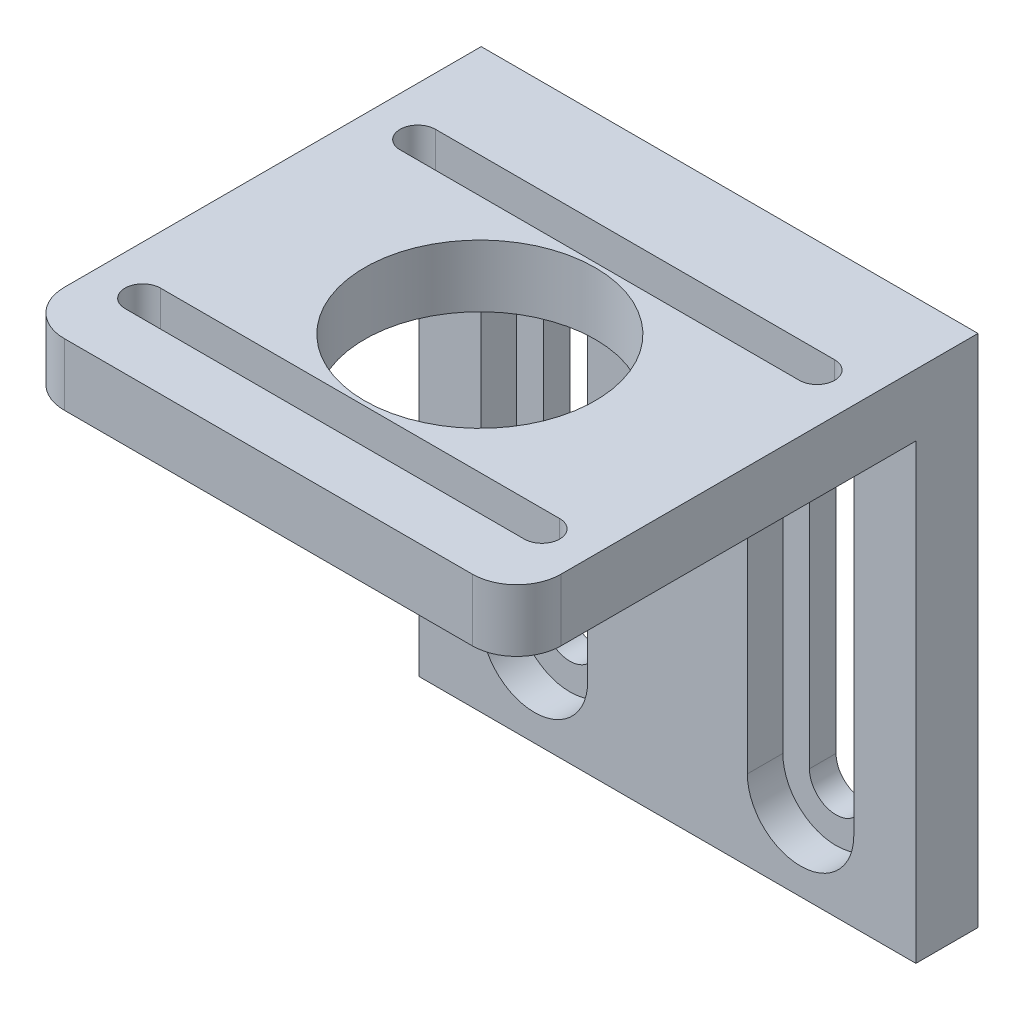
SolidWorks part; units mm, degrees
ref_plane "Front Plane" through (0, 0, 0) normal (0, 0, 1) x (1, 0, 0)
ref_plane "Top Plane" through (0, 0, 0) normal (0, 1, 0) x (1, 0, 0)
ref_plane "Right Plane" through (0, 0, 0) normal (1, 0, 0) x (0, 0, -1)
sketch "Esboço1" plane through (0, 0, 0) normal (0, 0, 1) x (1, 0, 0)
  line L32 (-63.6703, 183.4684) -> (-63.6703, 125.4684)
  line L33 (-63.6703, 125.4684) -> (-7.6703, 125.4684)
  line L34 (-7.6703, 125.4684) -> (-7.6703, 183.4684)
  line L35 (-7.6703, 183.4684) -> (-63.6703, 183.4684)
extrude "Ressalto-extrusão1" add sketch "Esboço1" along normal blind 7
sketch "Esboço3" plane through (0, 0, 7) normal (0, 0, 1) x (1, 0, 0)
  line L14 (-47.6703, 134.4684) -> (-47.6703, 171.4684)
  line L15 (-53.6703, 171.4684) -> (-53.6703, 134.4684)
  line L16 (-47.6703, 134.4684) -> (-47.6703, 171.4684)
  line L17 (-53.6703, 171.4684) -> (-53.6703, 134.4684)
  line L31 (-23.6703, 171.4684) -> (-23.6703, 134.4684)
  line L32 (-17.6703, 134.4684) -> (-17.6703, 171.4684)
  line L33 (-23.6703, 171.4684) -> (-23.6703, 134.4684)
  line L34 (-17.6703, 134.4684) -> (-17.6703, 171.4684)
  arc A21 (-48.4342, 173.4684) -> (-50.6703, 174.4684) centre (-50.6703, 171.4684) ccw
  arc A22 (-47.6703, 171.4684) -> (-48.4342, 173.4684) centre (-50.6703, 171.4684) ccw
  arc A23 (-50.6703, 174.4684) -> (-52.9064, 173.4684) centre (-50.6703, 171.4684) ccw
  arc A24 (-52.9064, 173.4684) -> (-53.6703, 171.4684) centre (-50.6703, 171.4684) ccw
  arc A25 (-53.6703, 134.4684) -> (-47.6703, 134.4684) centre (-50.6703, 134.4684) ccw
  arc A26 (-48.4342, 173.4684) -> (-50.6703, 174.4684) centre (-50.6703, 171.4684) ccw
  arc A27 (-47.6703, 171.4684) -> (-48.4342, 173.4684) centre (-50.6703, 171.4684) ccw
  arc A28 (-50.6703, 174.4684) -> (-52.9064, 173.4684) centre (-50.6703, 171.4684) ccw
  arc A29 (-52.9064, 173.4684) -> (-53.6703, 171.4684) centre (-50.6703, 171.4684) ccw
  arc A30 (-53.6703, 134.4684) -> (-47.6703, 134.4684) centre (-50.6703, 134.4684) ccw
  arc A46 (-18.4342, 173.4684) -> (-20.6703, 174.4684) centre (-20.6703, 171.4684) ccw
  arc A47 (-17.6703, 171.4684) -> (-18.4342, 173.4684) centre (-20.6703, 171.4684) ccw
  arc A48 (-20.6703, 174.4684) -> (-22.9064, 173.4684) centre (-20.6703, 171.4684) ccw
  arc A49 (-22.9064, 173.4684) -> (-23.6703, 171.4684) centre (-20.6703, 171.4684) ccw
  arc A50 (-23.6703, 134.4684) -> (-17.6703, 134.4684) centre (-20.6703, 134.4684) ccw
  arc A51 (-18.4342, 173.4684) -> (-20.6703, 174.4684) centre (-20.6703, 171.4684) ccw
  arc A52 (-17.6703, 171.4684) -> (-18.4342, 173.4684) centre (-20.6703, 171.4684) ccw
  arc A53 (-20.6703, 174.4684) -> (-22.9064, 173.4684) centre (-20.6703, 171.4684) ccw
  arc A54 (-22.9064, 173.4684) -> (-23.6703, 171.4684) centre (-20.6703, 171.4684) ccw
  arc A55 (-23.6703, 134.4684) -> (-17.6703, 134.4684) centre (-20.6703, 134.4684) ccw
  dimension "D1" = 0
  dimension "D2" = 0
extrude "Corte-extrusão1" cut sketch "Esboço3" against normal blind 7
sketch "Esboço4" plane through (0, 0, 7) normal (0, 0, 1) x (1, 0, 0)
  line L0 (-7.6703, 125.4684) -> (-7.6703, 183.4684) construction
  line L1 (-63.6703, 183.4684) -> (-7.6703, 183.4684)
  line L2 (-63.6703, 183.4684) -> (-63.6703, 176.4684)
  line L3 (-63.6703, 176.4684) -> (-7.6703, 176.4684)
  line L4 (-7.6703, 183.4684) -> (-7.6703, 176.4684)
  dimension "D1" = 7
extrude "Ressalto-extrusão2" add sketch "Esboço4" along normal blind 45
sketch "Esboço5" plane through (0, 176.4684, 0) normal (0, -1, 0) x (1, 0, 0)
  line L8 (-63.6703, 7) -> (-7.6703, 7)
  line L9 (-7.6703, 7) -> (-7.6703, 52)
  line L10 (-7.6703, 52) -> (-63.6703, 52)
  line L11 (-63.6703, 52) -> (-63.6703, 7)
  line L15 (-63.6703, 52) -> (-63.6703, 7)
  circle A2 centre (-20.1703, 43.65) radius 2
  circle A3 centre (-20.1703, 43.65) radius 2
  circle A5 centre (-51.1703, 43.65) radius 2
  circle A6 centre (-51.1703, 43.65) radius 2
  circle A11 centre (-51.1703, 12.65) radius 2
  circle A12 centre (-51.1703, 12.65) radius 2
  circle A14 centre (-20.1703, 12.65) radius 2
  circle A15 centre (-20.1703, 12.65) radius 2
  circle A17 centre (-35.6703, 28.15) radius 13
  circle A18 centre (-35.6703, 28.15) radius 13
  dimension "D1" = 0
  dimension "D2" = 0
  dimension "D3" = 0
  dimension "D4" = 0
  dimension "D5" = 0
  dimension "D6" = 2
extrude "Corte-extrusão2" cut sketch "Esboço5" against normal blind 45 contours A18 | A6 | A3 | A12 | A15
sketch "Esboço6" plane through (0, 0, 7) normal (0, 0, 1) x (1, 0, 0)
  line L4 (-56.6703, 171.4684) -> (-56.6703, 134.4684)
  line L5 (-44.6703, 134.4684) -> (-44.6703, 171.4684)
  line L6 (-56.6703, 171.4684) -> (-56.6703, 134.4684)
  line L7 (-44.6703, 134.4684) -> (-44.6703, 171.4684)
  line L10 (-14.6703, 134.4684) -> (-14.6703, 171.4684)
  line L11 (-26.6703, 171.4684) -> (-26.6703, 134.4684)
  line L12 (-14.6703, 134.4684) -> (-14.6703, 171.4684)
  line L13 (-26.6703, 171.4684) -> (-26.6703, 134.4684)
  arc A4 (-56.6703, 134.4684) -> (-44.6703, 134.4684) centre (-50.6703, 134.4684) ccw
  arc A5 (-44.6703, 171.4684) -> (-56.6703, 171.4684) centre (-50.6703, 171.4684) ccw
  arc A6 (-56.6703, 134.4684) -> (-44.6703, 134.4684) centre (-50.6703, 134.4684) ccw
  arc A7 (-44.6703, 171.4684) -> (-56.6703, 171.4684) centre (-50.6703, 171.4684) ccw
  arc A10 (-26.6703, 134.4684) -> (-14.6703, 134.4684) centre (-20.6703, 134.4684) ccw
  arc A11 (-14.6703, 171.4684) -> (-26.6703, 171.4684) centre (-20.6703, 171.4684) ccw
  arc A12 (-26.6703, 134.4684) -> (-14.6703, 134.4684) centre (-20.6703, 134.4684) ccw
  arc A13 (-14.6703, 171.4684) -> (-26.6703, 171.4684) centre (-20.6703, 171.4684) ccw
  dimension "D1" = 3
  dimension "D2" = 3
extrude "Corte-extrusão3" cut sketch "Esboço6" against normal blind 4 and the other way blind 2
fillet "Filete1" radius 5 2 edges at (-63.6703, 179.9684, 52) (-7.6703, 179.9684, 52)
sketch "Esboço7" plane through (0, 183.4684, 0) normal (0, 1, 0) x (1, 0, 0)
  line L0 (-58.1703, -12.65) -> (-13.1703, -12.65) construction
  line L1 (-58.1703, -43.65) -> (-13.1703, -43.65) construction
  line L2 (-35.6703, 0) -> (-35.6703, -52) construction
  line L5 (-20.1703, -10.65) -> (-20.1703, -14.65) construction
  line L8 (-20.1703, -41.65) -> (-20.1703, -45.65) construction
  line L9 (-30.8, 0) -> (30.8, 0) construction
  line L10 (-12.6703, -52) -> (-58.6703, -52) construction
  line L11 (-58.1703, -12.65) -> (-13.1703, -12.65) construction
  line L12 (-58.1703, -10.65) -> (-13.1703, -10.65)
  line L13 (-58.1703, -14.65) -> (-13.1703, -14.65)
  line L14 (-13.1703, -43.65) -> (-58.1703, -43.65) construction
  line L15 (-13.1703, -45.65) -> (-58.1703, -45.65)
  line L16 (-13.1703, -41.65) -> (-58.1703, -41.65)
  circle A0 centre (-20.1703, -12.65) radius 2 construction
  circle A1 centre (-20.1703, -43.65) radius 2 construction
  arc A2 (-58.1703, -10.65) -> (-58.1703, -14.65) centre (-58.1703, -12.65) ccw
  arc A3 (-13.1703, -14.65) -> (-13.1703, -10.65) centre (-13.1703, -12.65) ccw
  arc A4 (-13.1703, -45.65) -> (-13.1703, -41.65) centre (-13.1703, -43.65) ccw
  arc A5 (-58.1703, -41.65) -> (-58.1703, -45.65) centre (-58.1703, -43.65) ccw
  point P4 (-35.6703, -12.65)
  point P14 (-20.1703, -12.65)
  point P21 (-20.1703, -43.65)
  point P22 (-35.6703, -12.65)
  point P27 (-35.6703, -43.65)
  point P32 (0, 0)
  point P33 (0, 0)
  point P34 (0, 0)
  point P35 (-68.0821, -33.6505)
  dimension "D1" = 45
  dimension "D2" = 45
extrude "Corte-extrusão4" cut sketch "Esboço7" against normal blind 10
